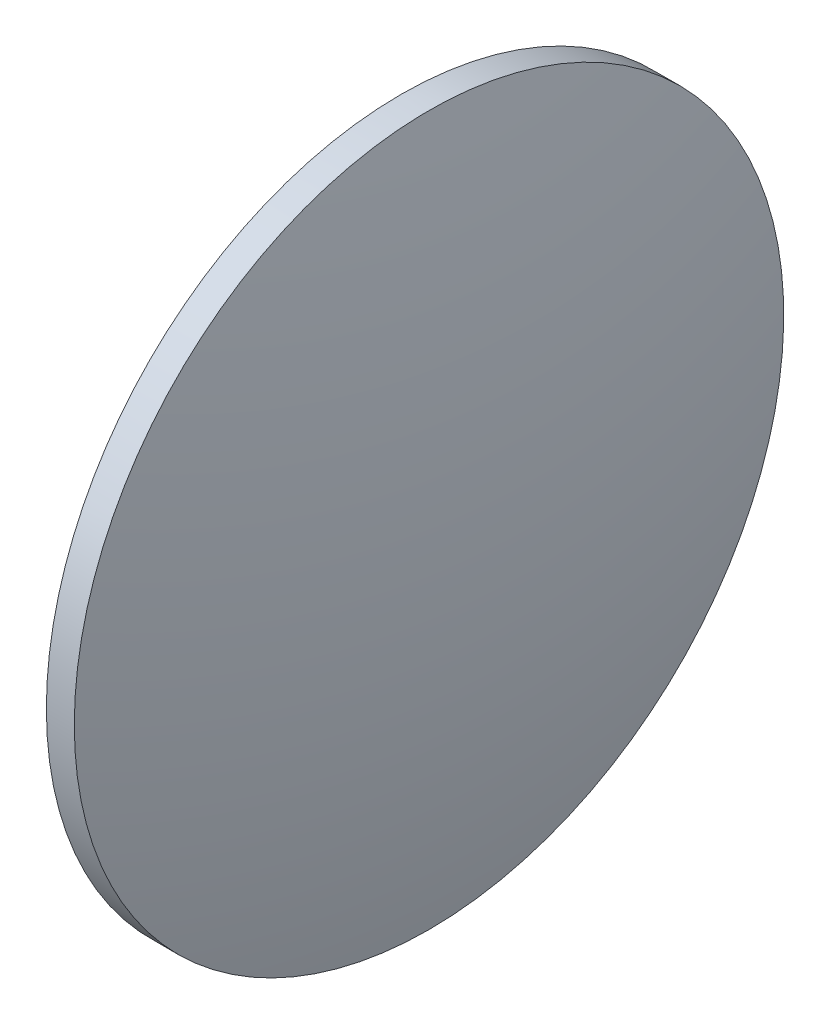
SolidWorks part; units mm, degrees
ref_plane "前视基准面" through (0, 0, 0) normal (0, 0, 1) x (1, 0, 0)
ref_plane "上视基准面" through (0, 0, 0) normal (0, 1, 0) x (1, 0, 0)
ref_plane "右视基准面" through (0, 0, 0) normal (1, 0, 0) x (0, 0, -1)
sketch "草图1" plane through (0, 0, 0) normal (0, 0, 1) x (1, 0, 0)
  line L0 (79.3054, 48.6161) -> (93.4772, 48.6161) construction
  line L1 (85.9582, 61.3161) -> (86.9582, 61.3161)
  line L2 (86.9582, 61.3161) -> (86.9582, 35.9161)
  line L3 (86.9582, 35.9161) -> (85.9582, 35.9161)
  line L4 (85.9582, 35.9161) -> (85.9582, 61.3161)
  arc A0 (85.9582, 61.3161) -> (85.9582, 35.9161) centre (139.7093, 48.6161) ccw
  arc A1 (86.9582, 35.9161) -> (86.9582, 61.3161) centre (33.2071, 48.6161) ccw
  dimension "D1" = 25.4
  dimension "D2" = 1
revolve "旋转1" add sketch "草图1" angle 360 about L0
